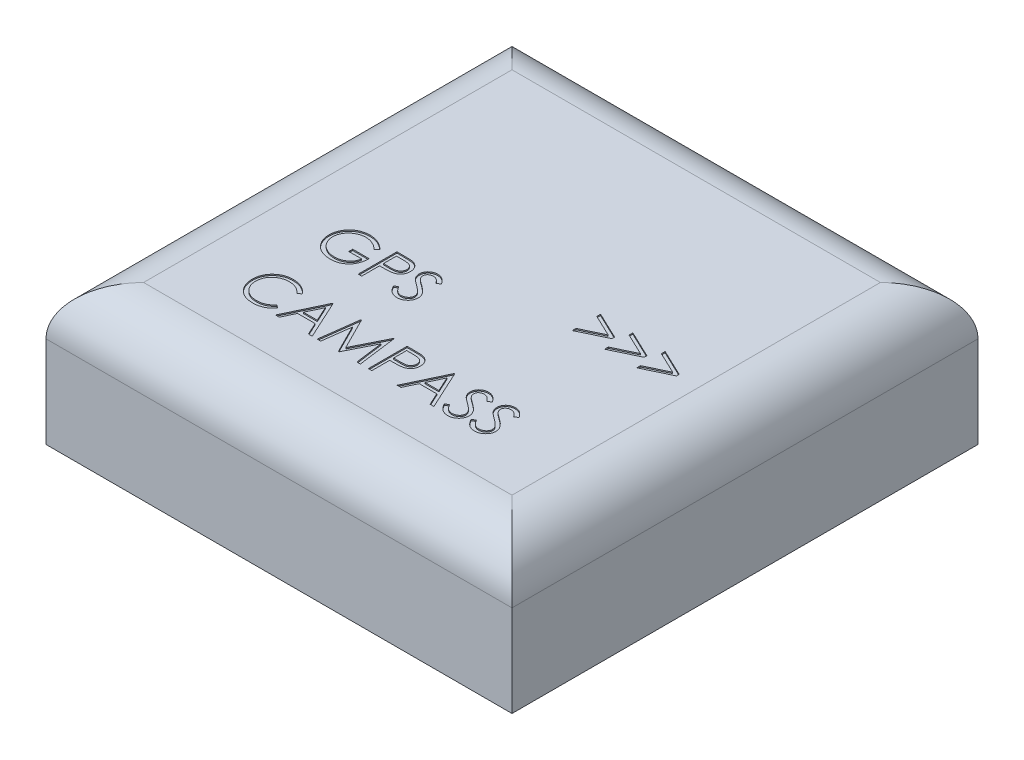
SolidWorks part; units mm, degrees
ref_plane "Front Plane" through (0, 0, 0) normal (0, 0, 1) x (1, 0, 0)
ref_plane "Top Plane" through (0, 0, 0) normal (0, 1, 0) x (1, 0, 0)
ref_plane "Right Plane" through (0, 0, 0) normal (1, 0, 0) x (0, 0, -1)
sketch "Sketch2" plane through (0, 0, 0) normal (0, 1, 0) x (1, 0, 0)
  line L1 (-19.1, 19.1) -> (19.1, 19.1)
  line L2 (-19.1, 19.1) -> (-19.1, -19.1)
  line L3 (-19.1, -19.1) -> (19.1, -19.1)
  line L4 (19.1, 19.1) -> (19.1, -19.1)
  line L5 (-19.1, 19.1) -> (19.1, -19.1) construction
  line L6 (-19.1, -19.1) -> (19.1, 19.1) construction
  point P0 (0, 0)
  dimension "D1" = 38.2
  dimension "D2" = 38.2
extrude "Boss-Extrude1" add sketch "Sketch2" along normal blind 11.5
sketch "Sketch4" plane through (0, 11.5, 0) normal (0, 1, 0) x (1, 0, 0)
  text T0 ">>>"
  text T1 "GPS\r\nCAMPASS"
extrude "Cut-Extrude1" cut sketch "Sketch4" against normal blind 0.1
fillet "Fillet1" radius 4 4 edges at (0, 11.5, -19.1) (19.1, 11.5, 0) (0, 11.5, 19.1) (-19.1, 11.5, 0)
sketch "Sketch5" plane through (-19.1, 0, 0) normal (-1, 0, 0) x (0, 0, 1)
  line L0 (0, 7.5) -> (0, 0) construction
  line L1 (19.1, 7.5) -> (-19.1, 7.5) construction
  line L2 (-19.1, 7.5) -> (-19.1, 0) construction
  line L3 (-5.8, 6) -> (3.6, 6)
  line L4 (-5.8, 6) -> (-5.8, 2)
  line L5 (-5.8, 2) -> (3.6, 2)
  line L6 (3.6, 6) -> (3.6, 2)
  line L7 (-5.8, 6) -> (3.6, 2) construction
  line L8 (-5.8, 2) -> (3.6, 6) construction
  line L9 (19.1, 7.5) -> (19.1, 0) construction
  line L10 (-19.1, 0) -> (19.1, 0) construction
  line L11 (-15.1, 11.5) -> (15.1, 11.5) construction
  point P5 (-1.1, 4)
  dimension "D1" = 13.3
  dimension "D2" = 15.5
  dimension "D3" = 2
  dimension "D4" = 5.5
extrude "Cut-Extrude2" cut sketch "Sketch5" against normal blind 3
